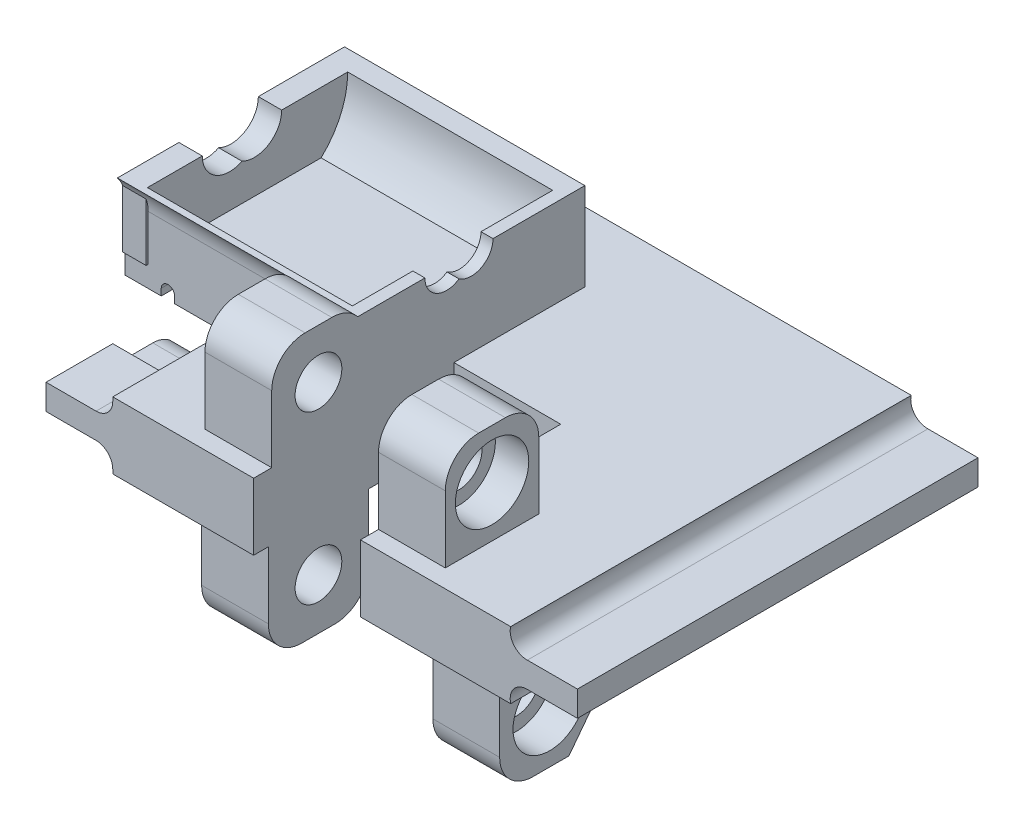
SolidWorks part; units mm, degrees
material "ABS"
ref_plane "정면" through (0, 0, 0) normal (0, 0, 1) x (1, 0, 0)
ref_plane "윗면" through (0, 0, 0) normal (0, 1, 0) x (1, 0, 0)
ref_plane "우측면" through (0, 0, 0) normal (1, 0, 0) x (0, 0, -1)
sketch "스케치1" plane through (0, 0, 0) normal (0, 0, 1) x (1, 0, 0)
  line L0 (0, 0) -> (0, 10)
  line L1 (29.8, 10) -> (-29.8, 10)
  line L2 (-32.3, 6.9) -> (-39.8, 6.9)
  line L3 (-39.8, 6.9) -> (-39.8, 3.1)
  line L4 (-39.8, 3.1) -> (-32.3, 3.1)
  line L5 (-29.8, 0) -> (29.8, 0)
  line L6 (39.8, 3.1) -> (32.3, 3.1)
  line L7 (39.8, 6.9) -> (39.8, 3.1)
  line L8 (32.3, 6.9) -> (39.8, 6.9)
  line L9 (-29.8, 10) -> (-29.8, 9.4)
  line L10 (-29.8, 0.6) -> (-29.8, 0)
  arc A2 (32.3, 3.1) -> (29.8, 0) centre (32.2267, 0.6011) ccw
  arc A3 (29.8, 10) -> (32.3, 6.9) centre (32.2267, 9.3989) ccw
  arc A5 (-32.3, 3.1) -> (-29.8, 0.6) centre (-32.3, 0.6) cw
  arc A6 (-29.8, 9.4) -> (-32.3, 6.9) centre (-32.3, 9.4) cw
  point P13 (0, 5)
  point P14 (-39.8, 5)
  point P15 (0, 0)
  dimension "D5" = 2.5
  dimension "D6" = 2.5
  dimension "D1" = 39.8
  dimension "D2" = 29.8
  dimension "D3" = 10
  dimension "D4" = 29.8
  dimension "D7" = 3.8
extrude "보스-돌출1" add sketch "스케치1" along normal blind 60
sketch "스케치2" plane through (-39.8, 0, 0) normal (-1, 0, 0) x (0, 0, 1)
  line L1 (44, 4) -> (50, 4)
  line L2 (50, 4) -> (50, 8)
  line L3 (16, 4) -> (10, 4)
  line L4 (50, 8) -> (10, 8)
  line L5 (30, 8) -> (30, 0)
  line L6 (20, 0) -> (40, 0)
  line L7 (60, 6.9) -> (60, 3.1) construction
  line L8 (10, 4) -> (10, 8)
  line L9 (60, 0) -> (0, 0) construction
  arc A0 (40, 0) -> (44, 4) centre (44, 0) cw
  arc A1 (20, 0) -> (16, 4) centre (16, 0) ccw
  line M12 (0, 3.1) -> (60, 3.1)
  line M14 (60, 6.9) -> (0, 6.9)
  dimension "D4" = 4
  dimension "D1" = 4
  dimension "D2" = 4
  dimension "D3" = 10
  dimension "D5" = 20
  dimension "D6" = 10
extrude "컷-돌출1" cut sketch "스케치2" against normal blind 17.3 contours A1 L5 L8 L3 M12 M14 | L6 A0 L5 M12 | A0 L1 L2 L5 M12 M14
sketch "Sketch1" plane through (0, 10, 0) normal (0, 1, 0) x (1, 0, 0)
  line L0 (29.8, -60) -> (-29.8, -60) construction
  line L1 (7.3, -60) -> (-8.7, -60)
  line L2 (7.3, -60) -> (7.3, -30)
  line L3 (7.3, -30) -> (-8.7, -30)
  line L4 (-8.7, -60) -> (-8.7, -30)
  line L5 (29.8, -60) -> (29.8, 0) construction
  dimension "D1" = 22.5
  dimension "D2" = 30
  dimension "D3" = 16
extrude "Cut-Extrude1" cut sketch "Sketch1" against normal blind 10
sketch "Sketch2" plane through (7.3, 0, 0) normal (-1, 0, 0) x (0, 0, 1)
  line L0 (60, 10) -> (30, 10) construction
  line L6 (57.29, 10) -> (43.29, 10)
  line L7 (57.29, 10) -> (57.29, 20)
  line L8 (52.29, 25) -> (48.29, 25)
  line L9 (43.29, 10) -> (43.29, 20)
  circle A0 centre (50.29, 17.61) radius 3.5
  arc A3 (48.29, 25) -> (43.29, 20) centre (48.29, 20) ccw
  arc A4 (57.29, 20) -> (52.29, 25) centre (52.29, 20) ccw
  point P1 (50.29, 25)
  point P11 (43.29, 25)
  point P15 (57.29, 25)
  dimension "D1" = 7
  dimension "D2" = 14
  dimension "D6" = 5
  dimension "D3" = 7.61
  dimension "D4" = 9.71
  dimension "D5" = 15
extrude "Boss-Extrude1" add sketch "Sketch2" against normal blind 10
sketch "Sketch4" plane through (17.3, 0, 0) normal (1, 0, 0) x (0, 0, -1)
  circle A0 centre (-50.29, 17.61) radius 5.5
  dimension "D1" = 11
extrude "Cut-Extrude4" cut sketch "Sketch4" against normal blind 5
ref_plane "Plane1" through (-0.7, 0, 0) normal (-1, 0, 0) x (0, 0, 1)
mirror "Mirror1" about plane through (-0.7, 0, 0) normal (-1, 0, 0) of "Cut-Extrude4", "Boss-Extrude1"
sketch "Sketch5" plane through (-8.7, 0, 0) normal (1, 0, 0) x (0, 0, -1)
  line L0 (-30, 0) -> (-60, 0) construction
  line L1 (-60, 0) -> (-60, 10) construction
  line L3 (-57.79, 0) -> (-42.79, 0)
  line L4 (-57.79, 0) -> (-57.79, -10)
  line L5 (-52.79, -15) -> (-47.79, -15)
  line L6 (-42.79, 0) -> (-42.79, -10)
  circle A0 centre (-50.29, -7.39) radius 3.5
  arc A1 (-47.79, -15) -> (-42.79, -10) centre (-47.79, -10) ccw
  arc A2 (-57.79, -10) -> (-52.79, -15) centre (-52.79, -10) ccw
  point P10 (0, 0)
  point P11 (-50.29, -15)
  point P14 (-42.79, -15)
  point P17 (-57.79, -15)
  dimension "D1" = 7
  dimension "D6" = 5
  dimension "D2" = 7.39
  dimension "D3" = 9.71
  dimension "D4" = 15
  dimension "D5" = 15
extrude "Boss-Extrude2" add sketch "Sketch5" against normal blind 10
sketch "Sketch6" plane through (-18.7, 0, 0) normal (-1, 0, 0) x (0, 0, 1)
  circle A0 centre (50.29, -7.39) radius 5.5
  dimension "D1" = 11
extrude "Cut-Extrude5" cut sketch "Sketch6" against normal blind 5
ref_plane "Plane2" through (3.62, 0, 0) normal (1, 0, 0) x (0, 0, -1)
mirror "Mirror2" about plane through (3.62, 0, 0) normal (1, 0, 0) of "Cut-Extrude5", "Boss-Extrude2"
sketch "Sketch7" plane through (-8.7, 0, 0) normal (1, 0, 0) x (0, 0, -1)
  line L0 (-30, 0) -> (-30, 10) construction
  line L1 (-30, 10) -> (-43.29, 10) construction
  line L2 (-39.4263, 14) -> (-17.3937, 14)
  line L4 (-39.0893, 32.6025) -> (-17.7307, 32.6025)
  line L8 (-44.4305, 23.15) -> (-10.3854, 23.15)
  line L9 (-44.4305, 36.3) -> (-10.3854, 36.3)
  line L10 (-44.4305, 36.3) -> (-44.4305, 10)
  line L11 (-44.4305, 10) -> (-10.3854, 10)
  line L12 (-10.3854, 36.3) -> (-10.3854, 10)
  arc A1 (-17.3937, 14) -> (-17.7307, 32.6025) centre (-25.91, 23.15) ccw
  arc A2 (-39.0893, 32.6025) -> (-39.4263, 14) centre (-30.91, 23.15) ccw
  point P7 (0, 0)
  point P11 (0, 0)
  point P12 (0, 0)
  point P19 (0, 0)
  dimension "D2" = 12.5
  dimension "D6" = 12.5
  dimension "D1" = 4.09
  dimension "D3" = 4
  dimension "D4" = 5
  dimension "D5" = 22.6025
extrude "Boss-Extrude4" add sketch "Sketch7" against normal blind 36
sketch "Sketch8" plane through (0, 23.15, 0) normal (0, 1, 0) x (1, 0, 0)
  line L1 (-8.7, -13.41) -> (-10.5, -13.41)
  line L2 (-8.7, -13.41) -> (-8.7, -43.7854)
  line L3 (-8.7, -43.7854) -> (-10.5, -43.7854)
  line L4 (-10.5, -13.41) -> (-10.5, -43.7854)
  line L6 (-44.7, -13.41) -> (-41.2, -13.41)
  line L7 (-44.7, -13.41) -> (-44.7, -43.6149)
  line L8 (-44.7, -43.6149) -> (-41.2, -43.6149)
  line L9 (-41.2, -13.41) -> (-41.2, -43.6149)
  dimension "D1" = 1.8
  dimension "D2" = 3.5
extrude "Boss-Extrude5" add sketch "Sketch8" against normal blind 10
sketch "Sketch9" plane through (-8.7, 0, 0) normal (1, 0, 0) x (0, 0, -1)
  line L0 (-44.407, 23.15) -> (-10.3854, 23.15) construction
  line L1 (-44.407, 23.15) -> (-10.3854, 23.15) construction
  circle A0 centre (-27.3962, 23.15) radius 3.25
  circle A1 centre (-31.0962, 23.15) radius 3.25
  line M2 (-10.3854, 23.15) -> (-44.407, 23.15)
  dimension "D1" = 6.5
  dimension "D2" = 6.5
  dimension "D3" = 3.7
extrude "Cut-Extrude6" cut sketch "Sketch9" against normal blind 10 contours A1 A0 M2 | A1 A0 M2
sketch "Sketch10" plane through (-44.7, 0, 0) normal (-1, 0, 0) x (0, 0, 1)
  line L0 (44.407, 23.15) -> (10.3854, 23.15) construction
  line L1 (44.407, 23.15) -> (10.3854, 23.15) construction
  circle A0 centre (27.3962, 23.15) radius 4.1
  circle A1 centre (31.0962, 23.15) radius 4.1
  line M10 (44.407, 23.15) -> (10.3854, 23.15)
  dimension "D1" = 8.2
  dimension "D2" = 8.2
  dimension "D3" = 3.7
extrude "Cut-Extrude7" cut sketch "Sketch10" against normal blind 10 contours A1 A0 M10 | A1 A0 M10 | A0 A1 M10
sketch "Sketch11" plane through (0, 0, 43.29) normal (0, 0, 1) x (1, 0, 0)
  line L0 (-39.25, 10) -> (-39.25, 11)
  line L2 (-37.25, 11) -> (-37.25, 10)
  line L3 (-37.25, 10) -> (-39.25, 10)
  arc A0 (-39.25, 11) -> (-37.25, 11) centre (-38.25, 11) cw
  dimension "D1" = 1
  dimension "D2" = 1
  dimension "D3" = 2
extrude "Cut-Extrude8" cut sketch "Sketch11" against normal through all
sketch "Sketch12" plane through (25.94, 0, 0) normal (1, 0, 0) x (0, 0, -1)
  line L0 (-42.79, -8.9362) -> (-47.4024, -14.985)
  line L1 (-42.79, -10) -> (-42.79, 0) construction
  line L2 (-47.4024, -14.985) -> (-43.1675, -15.5436)
  line L3 (-43.1675, -15.5436) -> (-40.8892, -10)
  line L4 (-40.8892, -10) -> (-42.79, -8.9362)
  arc A0 (-47.79, -15) -> (-42.79, -10) centre (-47.79, -10) ccw construction
extrude "Cut-Extrude9" cut sketch "Sketch12" against normal blind 10
sketch "Sketch13" plane through (0, 0, 43.29) normal (0, 0, 1) x (1, 0, 0)
  line L0 (-29.8, 10) -> (-23.7804, 10)
  line L1 (-29.8, 10) -> (-18.7, 10) construction
  line L2 (-23.7804, 10) -> (-23.7804, 11.1029)
  line L3 (-21.7804, 11.1029) -> (-21.7804, 9)
  line L4 (-21.7804, 9) -> (-30.476, 9)
  line L5 (-30.476, 9) -> (-29.8, 10)
  arc A0 (-23.7804, 11.1029) -> (-21.7804, 11.1029) centre (-22.7804, 11.1029) cw
  dimension "D2" = 1
  dimension "D1" = 1
extrude "Cut-Extrude10" cut sketch "Sketch13" against normal blind 35 and the other way blind 2
